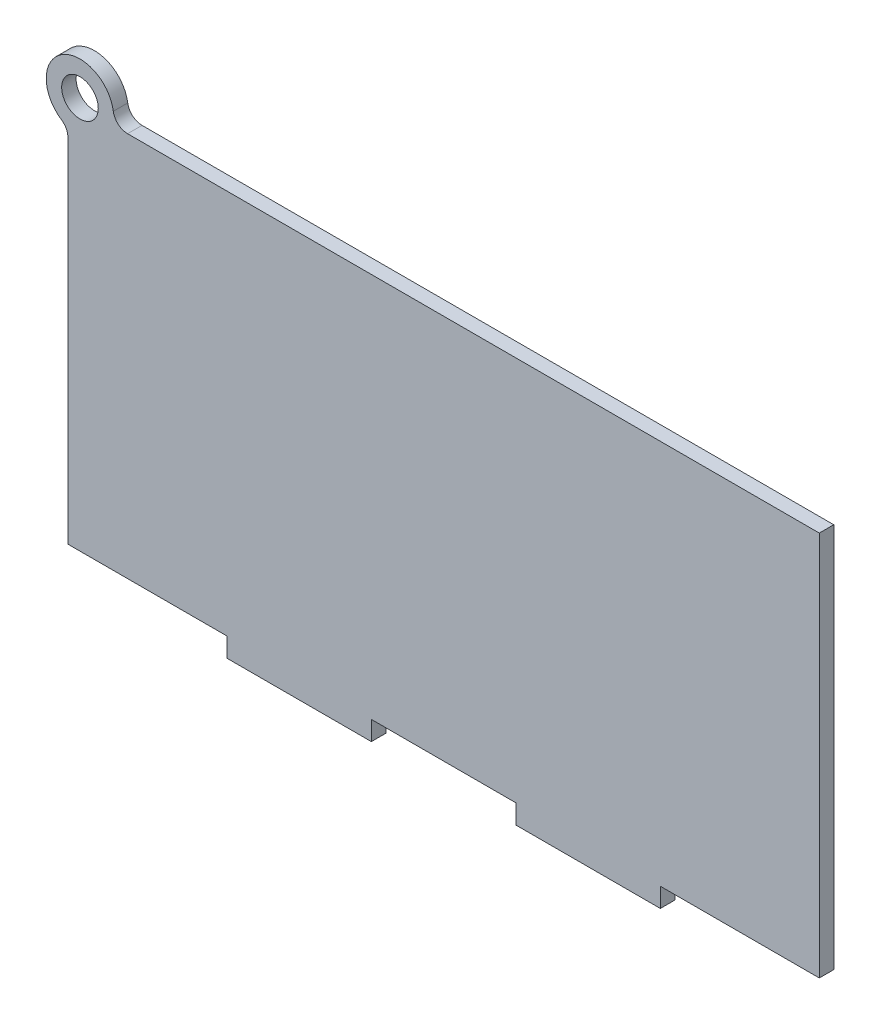
SolidWorks part; units mm, degrees
ref_plane "Front Plane" through (0, 0, 0) normal (0, 0, 1) x (1, 0, 0)
ref_plane "Top Plane" through (0, 0, 0) normal (0, 1, 0) x (1, 0, 0)
ref_plane "Right Plane" through (0, 0, 0) normal (1, 0, 0) x (0, 0, -1)
sketch "Sketch1" plane through (0, 0, 0) normal (0, 0, 1) x (1, 0, 0)
  line L0 (-45.4462, -41.8162) -> (-45.4462, -37.8162)
  line L2 (77.5538, -37.8162) -> (77.5538, 42.1838)
  line L3 (77.5538, 42.1838) -> (-66.0594, 42.1838)
  line L4 (-78.4462, -37.8162) -> (-78.4462, 35.3321)
  line L5 (77.7623, -41.816) -> (-78.4462, 42.1838) construction
  line L6 (77.5538, 42.1838) -> (-78.0896, -42.4752) construction
  line L9 (-78.4462, -37.8162) -> (-75.4462, -37.8162)
  line L11 (-15.4462, -41.8162) -> (-15.4462, -37.8162)
  line L12 (14.5538, -41.8162) -> (14.5538, -37.8162)
  line L13 (44.5538, -41.8162) -> (44.5538, -37.8162)
  line L14 (-15.4462, -37.8162) -> (14.5538, -37.8162)
  line L15 (-75.4462, -37.8162) -> (-45.4462, -37.8162)
  line L17 (-15.4462, -41.8162) -> (-45.4462, -41.8162)
  line L18 (44.5538, -41.8162) -> (14.5538, -41.8162)
  line L19 (44.5538, -37.8162) -> (77.5538, -37.8162)
  circle A0 centre (-75.9462, 43.6838) radius 3.8
  arc A1 (-69.0254, 44.7338) -> (-79.7962, 37.8376) centre (-75.9462, 43.6838) ccw
  arc A2 (-79.7962, 37.8376) -> (-78.4462, 35.3321) centre (-81.4462, 35.3321) cw
  arc A3 (-69.0254, 44.7338) -> (-66.0594, 42.1838) centre (-66.0594, 45.1838) ccw
  point P0 (0, 0)
  dimension "D4" = 3
  dimension "D1" = 156
  dimension "D2" = 84
  dimension "D3" = 3
extrude "Boss-Extrude1" add sketch "Sketch1" along normal blind 3
